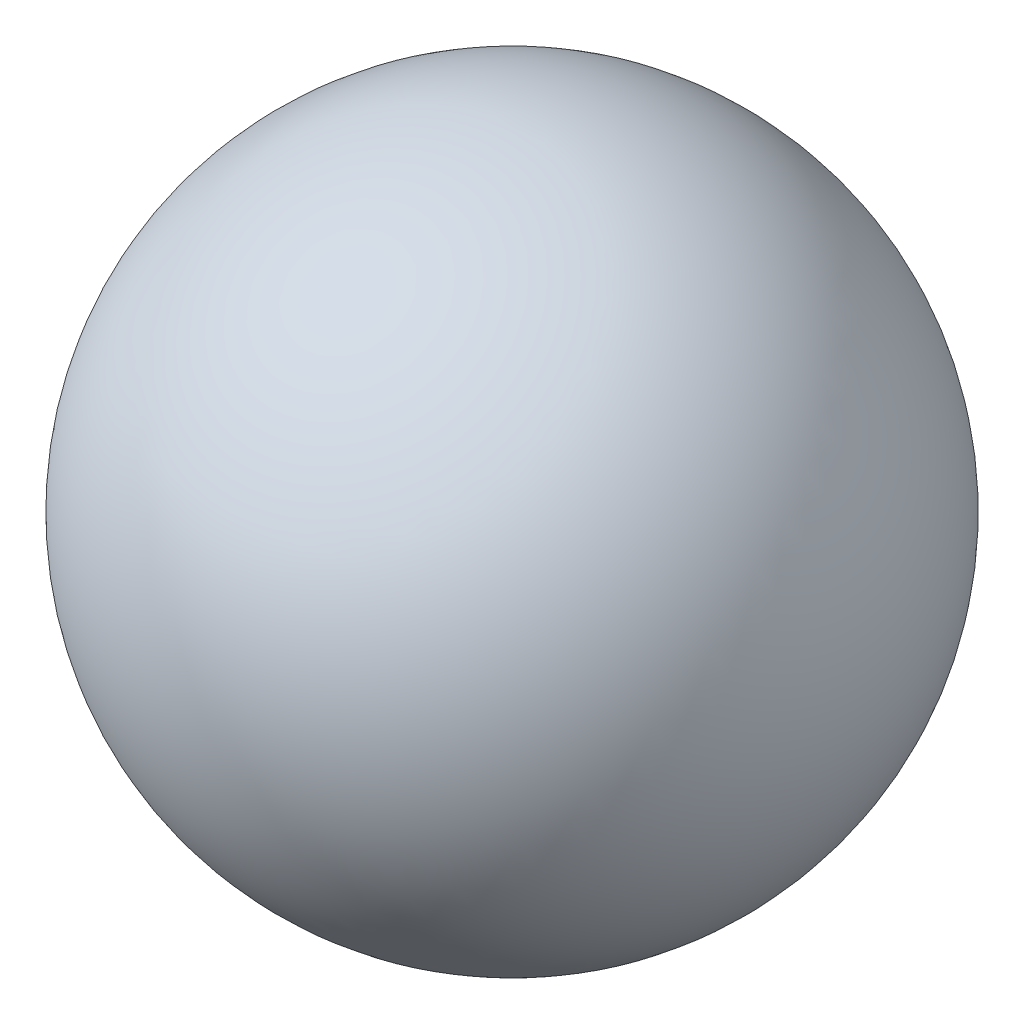
SolidWorks part; units mm, degrees
ref_plane "Front Plane" through (0, 0, 0) normal (0, 0, 1) x (1, 0, 0)
ref_plane "Top Plane" through (0, 0, 0) normal (0, 1, 0) x (1, 0, 0)
ref_plane "Right Plane" through (0, 0, 0) normal (1, 0, 0) x (0, 0, -1)
sketch "Sketch1" plane through (0, 0, 0) normal (0, 0, 1) x (1, 0, 0)
  line L0 (16.5929, 29.579) -> (16.5929, -30.421)
  arc A0 (16.5929, 29.579) -> (16.5929, -30.421) centre (16.5929, -0.421) cw
  dimension "D1" = 60
revolve "Revolve1" add sketch "Sketch1" angle 360 about L0
